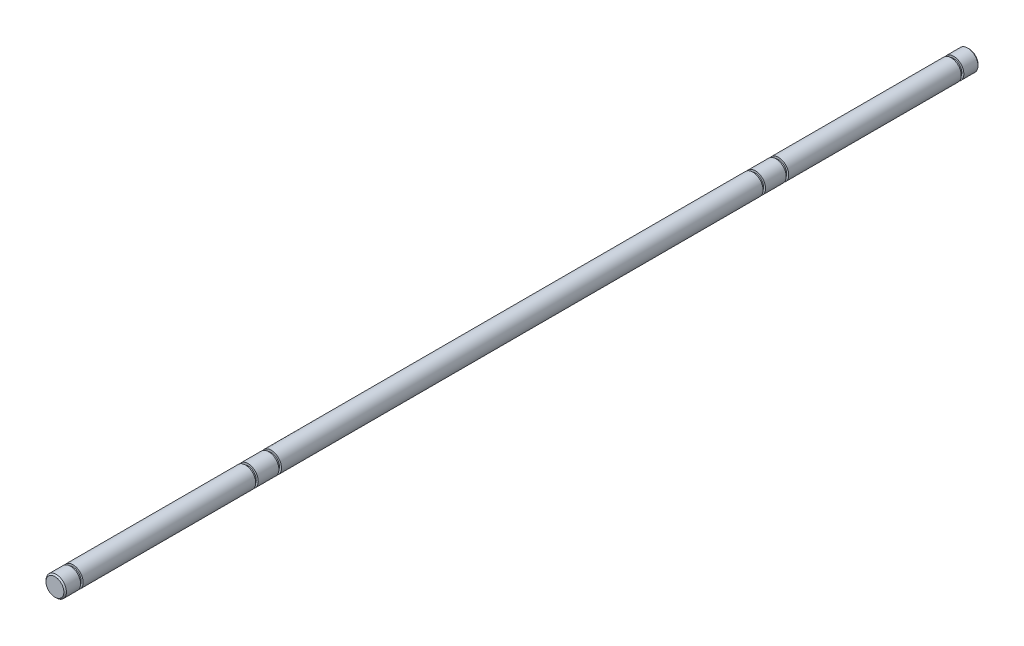
SolidWorks part; units mm, degrees
material "AISI 1020"
ref_plane "Alzado" through (0, 0, 0) normal (0, 0, 1) x (1, 0, 0)
ref_plane "Planta" through (0, 0, 0) normal (0, 1, 0) x (1, 0, 0)
ref_plane "Vista lateral" through (0, 0, 0) normal (1, 0, 0) x (0, 0, -1)
sketch "Croquis1" plane through (0, 0, 0) normal (0, 0, 1) x (1, 0, 0)
  circle A0 centre (0, 0) radius 3.99
  dimension "D1" = 7.98
extrude "Saliente-Extruir1" add sketch "Croquis1" along normal blind 355
sketch "Croquis2" plane through (0, 0, 0) normal (1, 0, 0) x (0, 0, -1)
  line L0 (0, 3.99) -> (-154.613, 3.99) construction
  line L2 (0, 3.99) -> (-355, 3.99) construction
  line L6 (-6, 3.99) -> (-7, 3.99)
  line L7 (-6, 3.99) -> (-6, 3.19)
  line L8 (-6, 3.19) -> (-7, 3.19)
  line L9 (-7, 3.99) -> (-7, 3.19)
  line L10 (-74, 3.99) -> (-75, 3.99)
  line L11 (-74, 3.99) -> (-74, 3.19)
  line L12 (-74, 3.19) -> (-75, 3.19)
  line L13 (-75, 3.99) -> (-75, 3.19)
  line L14 (-83, 3.99) -> (-84, 3.99)
  line L15 (-83, 3.99) -> (-83, 3.19)
  line L16 (-83, 3.19) -> (-84, 3.19)
  line L17 (-84, 3.99) -> (-84, 3.19)
  dimension "D1" = 1
  dimension "D2" = 6
  dimension "D3" = 1
  dimension "D4" = 67
  dimension "D5" = 8
  dimension "D6" = 1
  dimension "D7" = 0.8
  dimension "D8" = 0.8
  dimension "D9" = 0.8
ref_axis "Eje1" through (0, 0, 355) along (0, 0, -1)
revolve "Cortar-Revolución1" cut sketch "Croquis2" angle 360 about axis through (0, 0, 355) along (0, 0, -1)
ref_plane "Plano1" through (0, 0, 177.5) normal (0, 0, 1) x (1, 0, 0)
mirror "Simetría1" about plane through (0, 0, 177.5) normal (0, 0, 1) of "Cortar-Revolución1"
sketch "Croquis3" plane through (0, 0, 0) normal (0, 1, 0) x (1, 0, 0)
  line L1 (3.99, -74) -> (-3.99, -74)
  line L2 (3.99, -74) -> (3.99, 0)
  line L3 (3.99, 0) -> (-3.99, 0)
  line L4 (-3.99, -74) -> (-3.99, 0)
sketch "Croquis4" plane through (0, 0, 0) normal (0, 1, 0) x (1, 0, 0)
  line L1 (3.99, -281) -> (-3.99, -281)
  line L2 (3.99, -281) -> (3.99, -355)
  line L3 (3.99, -355) -> (-3.99, -355)
  line L4 (-3.99, -281) -> (-3.99, -355)
split line "Línea de partición1"
split line "Línea de partición2"
sketch "Croquis5" plane through (0, 0, 355) normal (0, 0, 1) x (1, 0, 0)
  circle A0 centre (0, 0) radius 3.9688
  circle A1 centre (0, 0) radius 3.99
  dimension "D1" = 7.9375
  dimension "D2" = 7.98
extrude "Cortar-Extruir1" cut sketch "Croquis5" against normal up to surface (84 mm away) up to face at (3.19, 0, 271)
sketch "Croquis6" plane through (0, 0, 0) normal (0, 0, -1) x (-1, 0, 0)
  circle A0 centre (0, 0) radius 3.99
  circle A1 centre (0, 0) radius 3.97
  dimension "D1" = 7.94
extrude "Cortar-Extruir2" cut sketch "Croquis6" against normal up to surface (84 mm away) up to face at (3.19, 0, 84)
chamfer "Chaflán1" distance 0.5 angle 45 2 edges at (-3.97, 0, 0) (3.9688, 0, 355)
